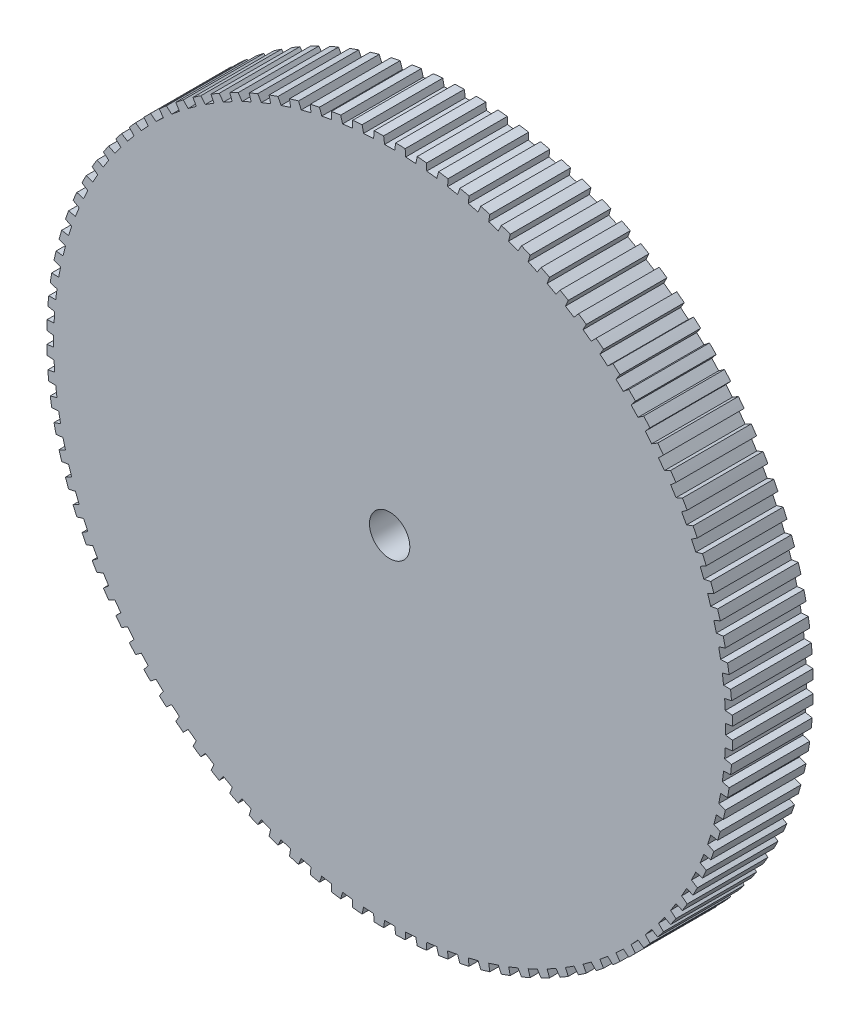
SolidWorks part; units mm, degrees
ref_plane "Front Plane" through (0, 0, 0) normal (0, 0, 1) x (1, 0, 0)
ref_plane "Top Plane" through (0, 0, 0) normal (0, 1, 0) x (1, 0, 0)
ref_plane "Right Plane" through (0, 0, 0) normal (1, 0, 0) x (0, 0, -1)
sketch "Sketch1" plane through (0, 0, 0) normal (0, 0, 1) x (1, 0, 0)
  circle A0 centre (0, 0) radius 37 construction
  circle A2 centre (0, 0) radius 34
  dimension "D1" = 74
  dimension "rubberthk" = 3
extrude "Boss-Extrude1" add sketch "Sketch1" along normal blind 8
sketch "Sketch4" plane through (0, 0, 0) normal (0, 0, -1) x (-1, 0, 0)
  circle A0 centre (0, 0) radius 4.85
  dimension "D1" = 9.7
extrude "Boss-Extrude2" add sketch "Sketch4" along normal blind 8
sketch "Sketch2" plane through (0, 0, 8) normal (0, 0, 1) x (1, 0, 0)
  circle A0 centre (0, 0) radius 4
  dimension "D1" = 8
extrude "Cut-Extrude1" cut sketch "Sketch2" against normal blind 4.35
sketch "Sketch5" plane through (0, 0, 3.65) normal (0, 0, 1) x (1, 0, 0)
  circle A0 centre (0, 0) radius 2
  dimension "D1" = 4
extrude "Cut-Extrude2" cut sketch "Sketch5" against normal offset from surface (4.15 mm away) 7.5 up to face at (-4.85, 0, -8)
sketch "Sketch6" plane through (0, 0, -8) normal (0, 0, -1) x (-1, 0, 0)
  line L0 (2.0785, 1.95) -> (-2.0785, 1.95)
  line L1 (-2.0785, -1.95) -> (2.0785, -1.95)
  arc A0 (2.0785, -1.95) -> (2.0785, 1.95) centre (0, 0) ccw
  arc A1 (-2.0785, 1.95) -> (-2.0785, -1.95) centre (0, 0) ccw
  dimension "D2" = 5.7
  dimension "D1" = 3.9
extrude "Cut-Extrude3" cut sketch "Sketch6" against normal up to surface (7.5 mm away) up to face at (-2, 0, -0.5)
sketch "Sketch7" plane through (0, 0, 8) normal (0, 0, 1) x (1, 0, 0)
  line L0 (-0.6, 33.9947) -> (-0.5, 33.31)
  line L1 (-0.5, 33.31) -> (0.5, 33.31)
  line L2 (0.5, 33.31) -> (0.6, 33.9947)
  line L3 (0, 0) -> (-0.6, 33.9947) construction
  line L4 (0, 0) -> (0.6, 33.9947) construction
  circle A0 centre (0, 0) radius 34 construction
  arc A1 (0.6, 33.9947) -> (-0.6, 33.9947) centre (0, 0) ccw
  point P8 (0, 33.31)
  dimension "D1" = 1
  dimension "D2" = 1.2
  dimension "D3" = 0.69
extrude "Cut-Extrude4" cut sketch "Sketch7" against normal through all
pattern_circular "CirPattern1" count 100 over 360 about axis through (0, 0, 0) along (0, 0, 1) of "Cut-Extrude4"
sketch "Sketch8" plane through (0, 0, 3.65) normal (0, 0, 1) x (1, 0, 0)
  circle A0 centre (0, 0) radius 2 construction
  circle A1 centre (0, 0) radius 4
  circle A2 centre (0, 0) radius 4
  circle A3 centre (0, 0) radius 2
  dimension "D1" = 0
extrude "ReverseCountersink" add sketch "Sketch8" along normal up to surface (4.35 mm away) up to face at (0, 0, 8)
equation "\"width\"= 24"
equation "\"thk\"= 3"
equation "\"holesize\"= 4.2"
equation "\"holedistance\"= ( 20 + 12 ) / 2"
equation "\"threaded_hole\"= 3.9"
equation "\"fillet_radius\"= 2"
equation "\"ground_clearance\"= 25"
equation "\"tire_thk\"= 3"
equation "\"innerwheel_diam\" = \"wheel_diam\"-2*\"tire_thk\""
equation "\"innerwheel_thk\"= 8"
equation "\"wheel_diam\"= 2*(\"width\"/2+\"ground_clearance\")"
equation "\"rubberthk@Sketch1\"=\"tire_thk\""
equation "\"D1@Boss-Extrude1\"=\"innerwheel_thk\""
equation "\"coloursensor_holesize\"= 2.65"
equation "\"hole_to_edge\" = 4"
equation "\"D1@Sketch1\"=\"wheel_diam\""
